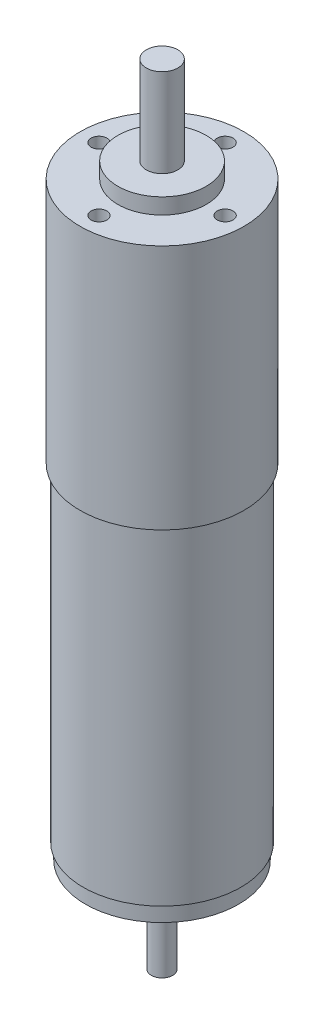
SolidWorks part; units mm, degrees
ref_plane "Face" through (0, 0, 0) normal (0, 0, 1) x (1, 0, 0)
ref_plane "Dessus" through (0, 0, 0) normal (0, 1, 0) x (1, 0, 0)
ref_plane "Droite" through (0, 0, 0) normal (1, 0, 0) x (0, 0, -1)
sketch "Esquisse1" plane through (0, 0, 0) normal (0, 0, 1) x (1, 0, 0)
  line L0 (0, 0) -> (0, 110) construction
  line L1 (0, 0) -> (12.15, 0)
  line L2 (12.15, 0) -> (12.15, 2.5)
  line L3 (12.15, 2.5) -> (12.5, 2.5)
  line L4 (12.5, 2.5) -> (12.5, 54.5)
  line L5 (12.5, 54.5) -> (13, 54.5)
  line L6 (13, 54.5) -> (13, 93.5)
  line L7 (13, 93.5) -> (7, 93.5)
  line L8 (7, 93.5) -> (7, 96)
  line L9 (7, 96) -> (2.5, 96)
  line L10 (2.5, 96) -> (2.5, 110)
  line L11 (2.5, 110) -> (0, 110)
  line L12 (0, 0) -> (0, 110)
  dimension "D1" = 5
  dimension "D2" = 25
  dimension "D3" = 26
  dimension "D4" = 54.5
  dimension "D5" = 14
  dimension "D6" = 14
  dimension "D7" = 2.5
  dimension "D8" = 39
  dimension "D9" = 24.3
  dimension "D10" = 2.5
revolve "Révolution1" add sketch "Esquisse1" angle 360 about L0
sketch "Esquisse2" plane through (0, 0, 0) normal (0, -1, 0) x (1, 0, 0)
  circle A0 centre (0, 0) radius 1.6928
extrude "Boss.-Extru.1" add sketch "Esquisse2" along normal blind 15
sketch "Esquisse3" plane through (0, 0, 0) normal (0, -1, 0) x (1, 0, 0)
  circle A0 centre (0, 0) radius 4
  dimension "D1" = 8
extrude "Boss.-Extru.2" add sketch "Esquisse3" along normal blind 2.5
sketch "Esquisse4" plane through (0, 93.5, 0) normal (0, 1, 0) x (1, 0, 0)
  line L0 (0, 0) -> (0, 13) construction
  line L1 (0, 0) -> (0, 10) construction
  circle A0 centre (0, 0) radius 13 construction
  circle A1 centre (0, 10) radius 1.25
  circle A2 centre (10, 0) radius 1.25
  circle A3 centre (0, -10) radius 1.25
  circle A4 centre (-10, 0) radius 1.25
  dimension "D1" = 2.5
  dimension "D2" = 10
  dimension "D4" = 10
  dimension "D3" = 4
extrude "Enlèv. mat.-Extru.1" cut sketch "Esquisse4" against normal blind 5
